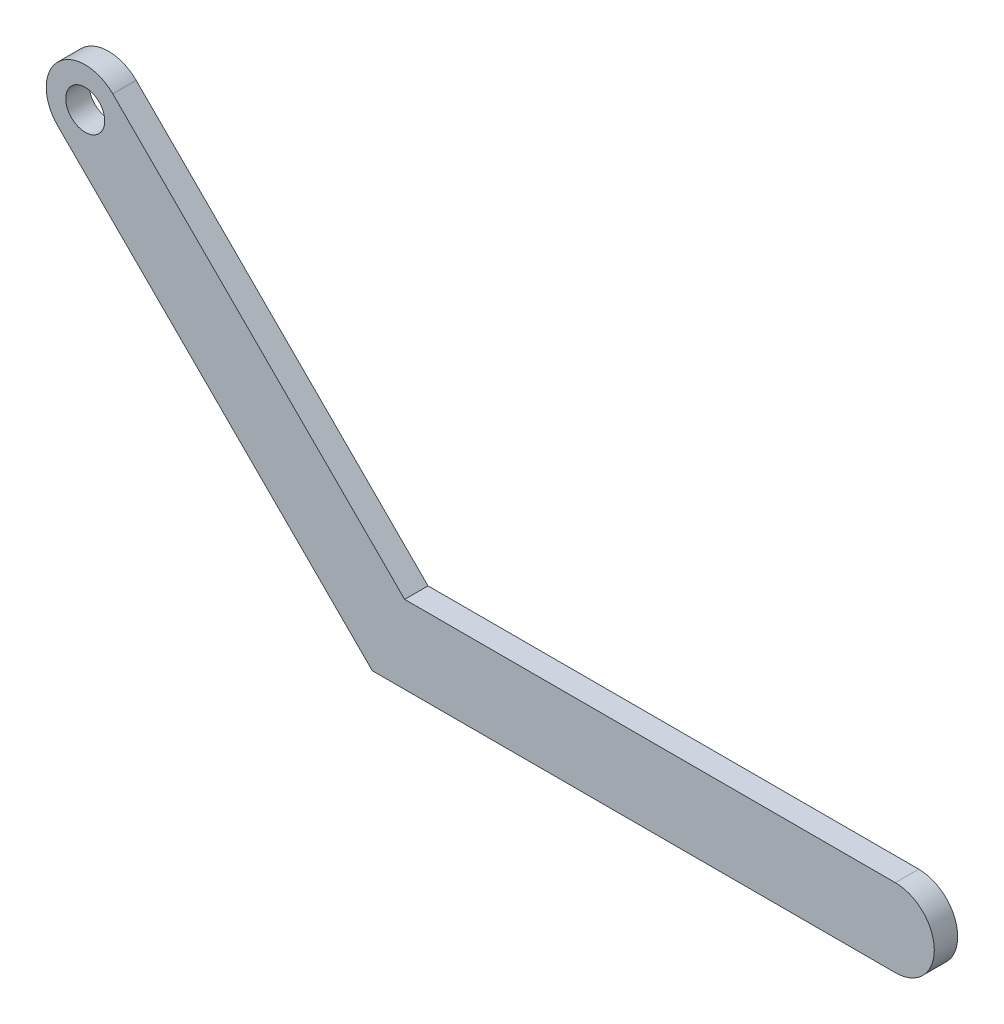
SolidWorks part; units mm, degrees
ref_plane "Front Plane" through (0, 0, 0) normal (0, 0, 1) x (1, 0, 0)
ref_plane "Top Plane" through (0, 0, 0) normal (0, 1, 0) x (1, 0, 0)
ref_plane "Right Plane" through (0, 0, 0) normal (1, 0, 0) x (0, 0, -1)
sketch "Sketch2" plane through (0, 0, 0) normal (0, 0, 1) x (1, 0, 0)
  line L0 (0, 0) -> (-38.8909, 38.8909) construction
  line L1 (-38.8909, 38.8909) -> (0, 0) construction
  line L2 (0, 0) -> (65, 0) construction
  line L3 (2.0711, 5) -> (65, 5)
  line L4 (2.0711, 5) -> (-35.3553, 42.4264)
  line L5 (-2.0711, -5) -> (65, -5)
  line L6 (-2.0711, -5) -> (-42.4264, 35.3553)
  arc A0 (-35.3553, 42.4264) -> (-42.4264, 35.3553) centre (-38.8909, 38.8909) ccw
  arc A1 (65, 5) -> (65, -5) centre (65, 0) cw
  point P12 (0, 0)
  dimension "D1" = 55
  dimension "D2" = 65
  dimension "D3" = 135
  dimension "D4" = 5
  dimension "D5" = 5
extrude "Boss-Extrude1" add sketch "Sketch2" along normal blind 3
sketch "Sketch3" plane through (0, 0, 3) normal (0, 0, 1) x (1, 0, 0)
  circle A0 centre (-38.8909, 38.8909) radius 2.5
extrude "Cut-Extrude1" cut sketch "Sketch3" against normal blind 11
